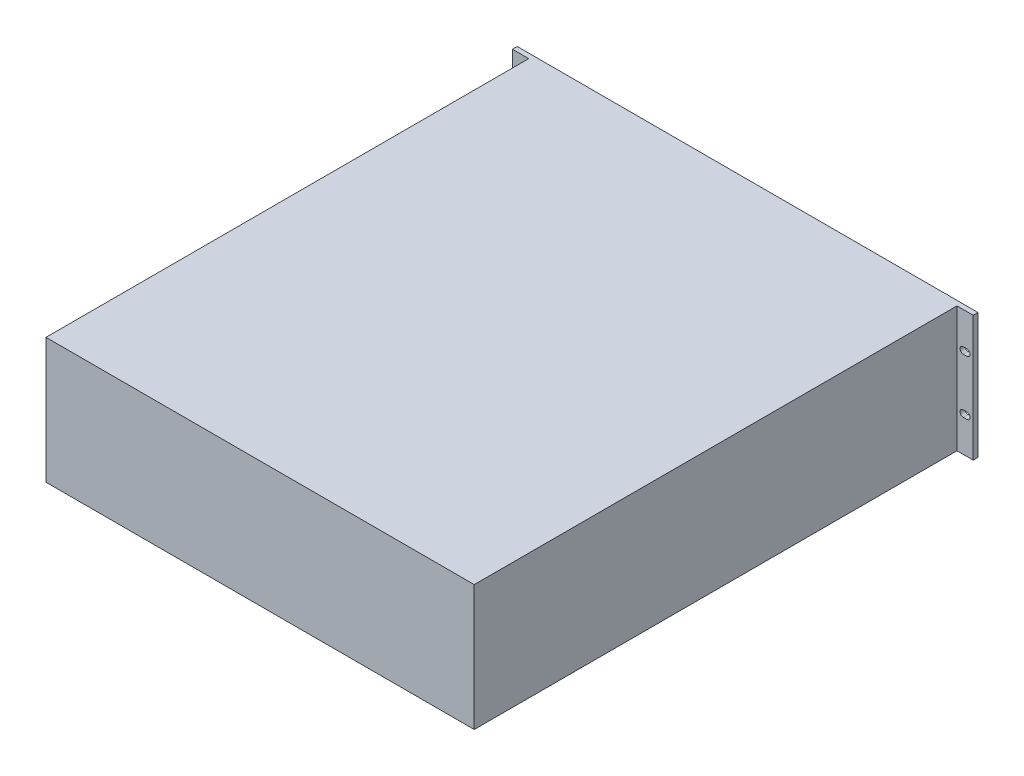
SolidWorks part; units mm, degrees
ref_plane "Front Plane" through (0, 0, 0) normal (0, 0, 1) x (1, 0, 0)
ref_plane "Top Plane" through (0, 0, 0) normal (0, 1, 0) x (1, 0, 0)
ref_plane "Right Plane" through (0, 0, 0) normal (1, 0, 0) x (0, 0, -1)
sketch "Sketch1" plane through (0, 0, 0) normal (0, 0, 1) x (1, 0, 0)
  line L1 (224, -65.65) -> (-224, -65.65)
  line L2 (224, -65.65) -> (224, 65.65)
  line L3 (224, 65.65) -> (-224, 65.65)
  line L4 (-224, -65.65) -> (-224, 65.65)
  line L5 (224, -65.65) -> (-224, 65.65) construction
  line L6 (224, 65.65) -> (-224, -65.65) construction
  point P0 (0, 0)
  dimension "D1" = 448
  dimension "D2" = 131.3
extrude "Boss-Extrude1" add sketch "Sketch1" along normal blind 510
sketch "Sketch2" plane through (0, 0, 0) normal (0, 0, -1) x (-1, 0, 0)
  line L0 (-224, 65.65) -> (224, 65.65) construction
  line L1 (241, -65.65) -> (-241, -65.65)
  line L2 (241, -65.65) -> (241, 65.65)
  line L3 (241, 65.65) -> (-241, 65.65)
  line L4 (-241, -65.65) -> (-241, 65.65)
  line L5 (241, -65.65) -> (-241, 65.65) construction
  line L6 (241, 65.65) -> (-241, -65.65) construction
  point P0 (0, 0)
  dimension "D1" = 482
extrude "Boss-Extrude2" add sketch "Sketch2" against normal blind 5
sketch "Sketch3" plane through (0, 0, 0) normal (0, 0, -1) x (-1, 0, 0)
  line L0 (-234.4, 28.575) -> (-230.6, 28.575) construction
  line L1 (-234.4, 31.975) -> (-230.6, 31.975)
  line L2 (-234.4, 25.175) -> (-230.6, 25.175)
  line L3 (234.4, 28.575) -> (230.6, 28.575) construction
  line L4 (234.4, 25.175) -> (230.6, 25.175)
  line L5 (234.4, 31.975) -> (230.6, 31.975)
  line L6 (-232.5, 28.575) -> (232.5, 28.575) construction
  line L7 (0, 0) -> (0, 28.575) construction
  line L8 (0, 0) -> (49.6428, 0) construction
  arc A0 (-234.4, 31.975) -> (-234.4, 25.175) centre (-234.4, 28.575) ccw
  arc A1 (-230.6, 25.175) -> (-230.6, 31.975) centre (-230.6, 28.575) ccw
  arc A2 (234.4, 25.175) -> (234.4, 31.975) centre (234.4, 28.575) ccw
  arc A3 (230.6, 31.975) -> (230.6, 25.175) centre (230.6, 28.575) ccw
  point P2 (-232.5, 28.575)
  point P8 (232.5, 28.575)
  point P14 (-237.8, 28.575)
  point P15 (-227.2, 28.575)
  dimension "D1" = 6.8
  dimension "D2" = 10.6
  dimension "D3" = 465
  dimension "D4" = 28.575
  dimension "D5" = 6.8
extrude "Cut-Extrude1" cut sketch "Sketch3" against normal through all
mirror "Mirror1" about plane through (0, 0, 0) normal (0, 1, 0) of "Cut-Extrude1"
